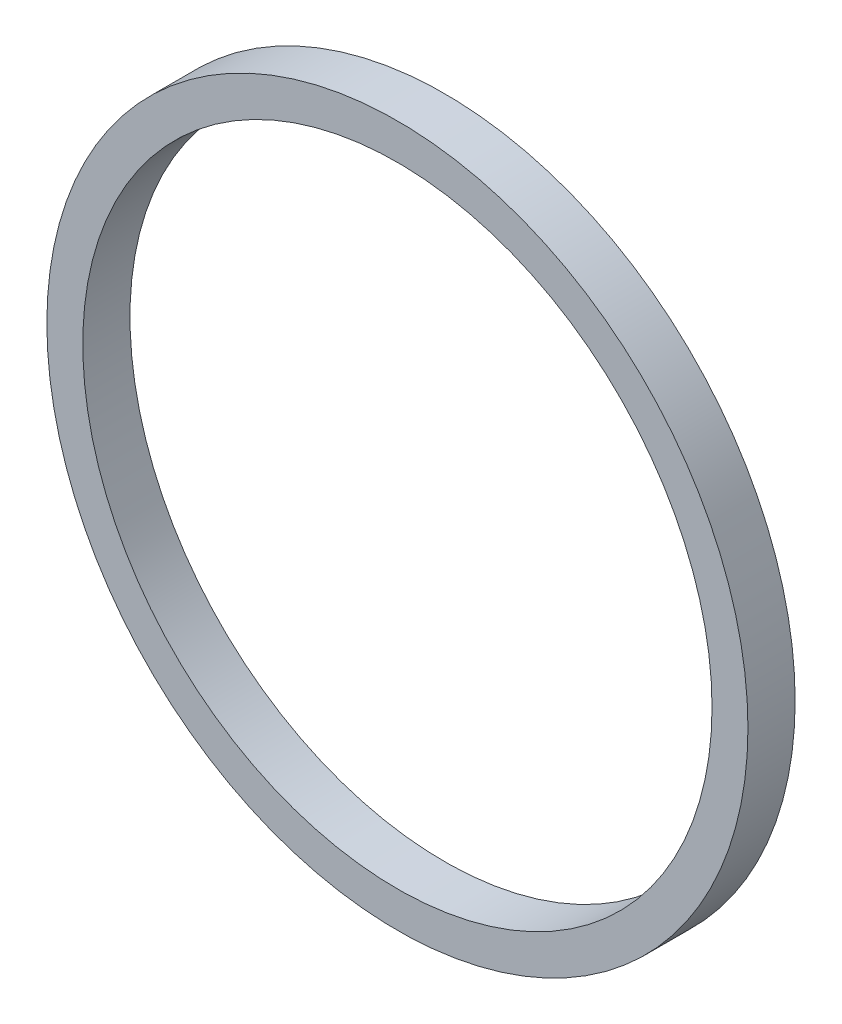
SolidWorks part; units mm, degrees
material "Copper"
ref_plane "Front Plane" through (0, 0, 0) normal (0, 0, 1) x (1, 0, 0)
ref_plane "Top Plane" through (0, 0, 0) normal (0, 1, 0) x (1, 0, 0)
ref_plane "Right Plane" through (0, 0, 0) normal (1, 0, 0) x (0, 0, -1)
sketch "Sketch1" plane through (0, 0, 0) normal (0, 0, 1) x (1, 0, 0)
  circle A0 centre (0, 0) radius 141.5
  circle A1 centre (0, 0) radius 127
  dimension "D1" = 14.5
extrude "Boss-Extrude1" add sketch "Sketch1" along normal blind 19.05
